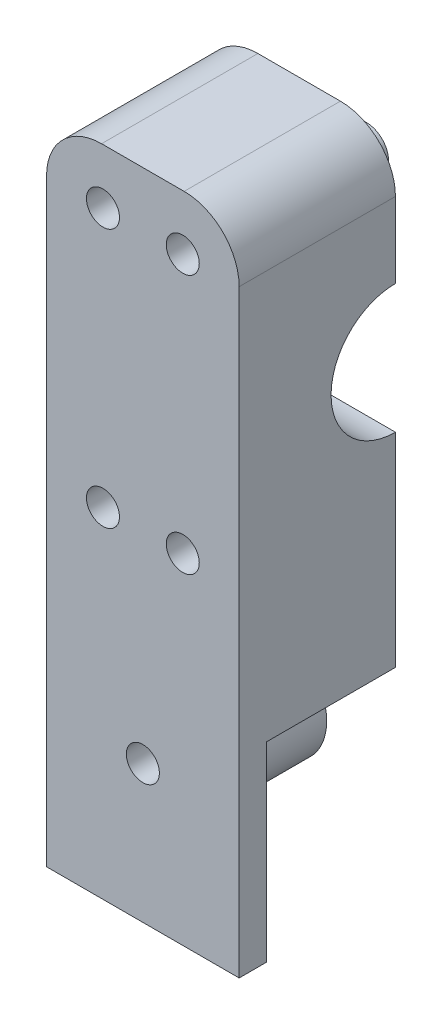
SolidWorks part; units mm, degrees
material "Nylon 6/10"
ref_plane "Front Plane" through (0, 0, 0) normal (0, 0, 1) x (1, 0, 0)
ref_plane "Top Plane" through (0, 0, 0) normal (0, 1, 0) x (1, 0, 0)
ref_plane "Right Plane" through (0, 0, 0) normal (1, 0, 0) x (0, 0, -1)
sketch "Sketch1" plane through (0, 0, 0) normal (1, 0, 0) x (0, 0, -1)
  line L1 (-28.4, -59.4) -> (-23.4, -59.4)
  line L2 (-28.4, -59.4) -> (-28.4, 59.4) construction
  line L3 (-28.4, 59.4) -> (28.4, 59.4)
  line L4 (28.4, -59.4) -> (28.4, 59.4) construction
  line L5 (-28.4, -59.4) -> (28.4, 59.4) construction
  line L6 (-28.4, 59.4) -> (28.4, -59.4) construction
  line L7 (28.4, 59.4) -> (28.4, -59.4)
  line L8 (-28.4, 59.4) -> (-28.4, -59.4)
  line L9 (-28.4, -14.4) -> (28.4, -14.4) construction
  line L10 (23.4, -59.4) -> (28.4, -59.4)
  line L11 (-23.4, -14.4) -> (23.4, -14.4)
  line L12 (-23.4, -14.4) -> (-23.4, -59.4)
  line L14 (23.4, -14.4) -> (23.4, -59.4)
  circle A0 centre (0, 24) radius 12.7 construction
  circle A1 centre (0, 24) radius 11.7
  point P0 (0, 0)
  dimension "D3" = 25.4
  dimension "D5" = 45
  dimension "D7" = 5
  dimension "D2" = 73.8
  dimension "D8" = 1
  dimension "D1" = 56.8
  dimension "D4" = 35.4
  dimension "D6" = 5
extrude "Boss-Extrude1" add sketch "Sketch1" along normal blind 35
sketch "Sketch2" plane through (0, 0, 28.4) normal (0, 0, 1) x (1, 0, 0)
  line L0 (35, -59.4) -> (0, -59.4) construction
  line L1 (0, -14.4) -> (35, -14.4) construction
  line L3 (0, -24.7175) -> (0, -13.4)
  line L4 (0, -59.4) -> (0, 59.4) construction
  line L5 (0, -13.4) -> (35, -13.4)
  line L6 (35, 59.4) -> (35, -59.4) construction
  line L7 (35, -13.4) -> (35, -24.7175)
  circle A0 centre (17.5, -34.4) radius 10
  arc A3 (35, -24.7175) -> (0, -24.7175) centre (17.5, -34.4) ccw
  point P4 (17.5, -59.4)
  dimension "D1" = 20
  dimension "D2" = 25
  dimension "D3" = 1
extrude "Boss-Extrude3" add sketch "Sketch2" against normal up to surface (51.8 mm away) up to face at (17.5, -36.9, -23.4)
sketch "Sketch3" plane through (0, 0, 28.4) normal (0, 0, 1) x (1, 0, 0)
  line L0 (0, 59.4) -> (0, -59.4) construction
  line L1 (35, 59.4) -> (0, 59.4) construction
  line L2 (35, 59.4) -> (35, -59.4) construction
  circle A0 centre (10.25, 49.4) radius 3
  circle A1 centre (17.5, -34.4) radius 3
  circle A2 centre (10.25, 2.3) radius 3
  circle A3 centre (24.75, 2.3) radius 3
  circle A4 centre (24.75, 49.4) radius 3
  dimension "D1" = 6
  dimension "D2" = 10
  dimension "D5" = 47.1
  dimension "D3" = 10.25
  dimension "D4" = 10.25
extrude "Cut-Extrude1" cut sketch "Sketch3" against normal through all both and the other way through all
ref_plane "Plane2" through (12.7375, 0, 0) normal (-1, 0, 0) x (0, 0, 1)
sketch "Sketch6" plane through (35, 0, 0) normal (1, 0, 0) x (0, 0, -1)
  line L0 (28.4, 59.4) -> (-28.4, 59.4) construction
  line L1 (0, 59.4) -> (28.4, 59.4)
  line L2 (0, 59.4) -> (0, -59.4)
  line L3 (0, -59.4) -> (28.4, -59.4)
  line L4 (28.4, 59.4) -> (28.4, -59.4)
extrude "Cut-Extrude3" cut sketch "Sketch6" against normal through all
sketch "Sketch7" plane through (0, 0, 0) normal (0, 0, -1) x (-1, 0, 0)
  circle A0 centre (-24.75, 49.4) radius 4
  circle A1 centre (-10.25, 49.4) radius 4
  circle A2 centre (-24.75, 2.3) radius 4
  circle A3 centre (-10.25, 2.3) radius 4
  circle A5 centre (-24.75, 49.4) radius 3 construction
  circle A6 centre (-24.75, 2.3) radius 3 construction
  circle A7 centre (-24.75, 49.4) radius 3
  circle A8 centre (-10.25, 49.4) radius 3
  circle A9 centre (-10.25, 2.3) radius 3
  circle A10 centre (-24.75, 2.3) radius 3
  dimension "D1" = 1
sketch "Sketch8" plane through (0, 0, 0) normal (0, 0, -1) x (-1, 0, 0)
  circle A0 centre (-17.5, -34.4) radius 10
  circle A1 centre (-17.5, -34.4) radius 3
  circle A4 centre (-17.5, -34.4) radius 3 construction
  dimension "D1" = 20
extrude "Cut-Extrude4" cut sketch "Sketch8" against normal blind 5
extrude "Boss-Extrude4" add sketch "Sketch7" along normal blind 5
fillet "Fillet1" radius 10 2 edges at (35, 59.4, 14.2) (0, 59.4, 14.2)
equation "\"keelOutDiameter\"= 1in"
equation "\"keelInDiameter\"= \"keelOutDiameter\" - 0.125in"
equation "\"frontBoltClearance\"= 7.25mm"
equation "\"betweenBoltsDistance\"= 20mm"
equation "\"wingLength\"= 1.4m"
equation "\"frontTubeLength\"= \"wingLength\" / sin ( 34.95deg )"
equation "\"plateThickness\"= 5mm"
equation "\"crossBarOutDiameter\"= 1in"
equation "\"crossBarInDiameter\"= \"crossBarOutDiameter\" - 0.125in"
equation "\"frontToCrossBar\"= 466mm"
equation "\"D3@Sketch1\"=\"keelOutDiameter\""
